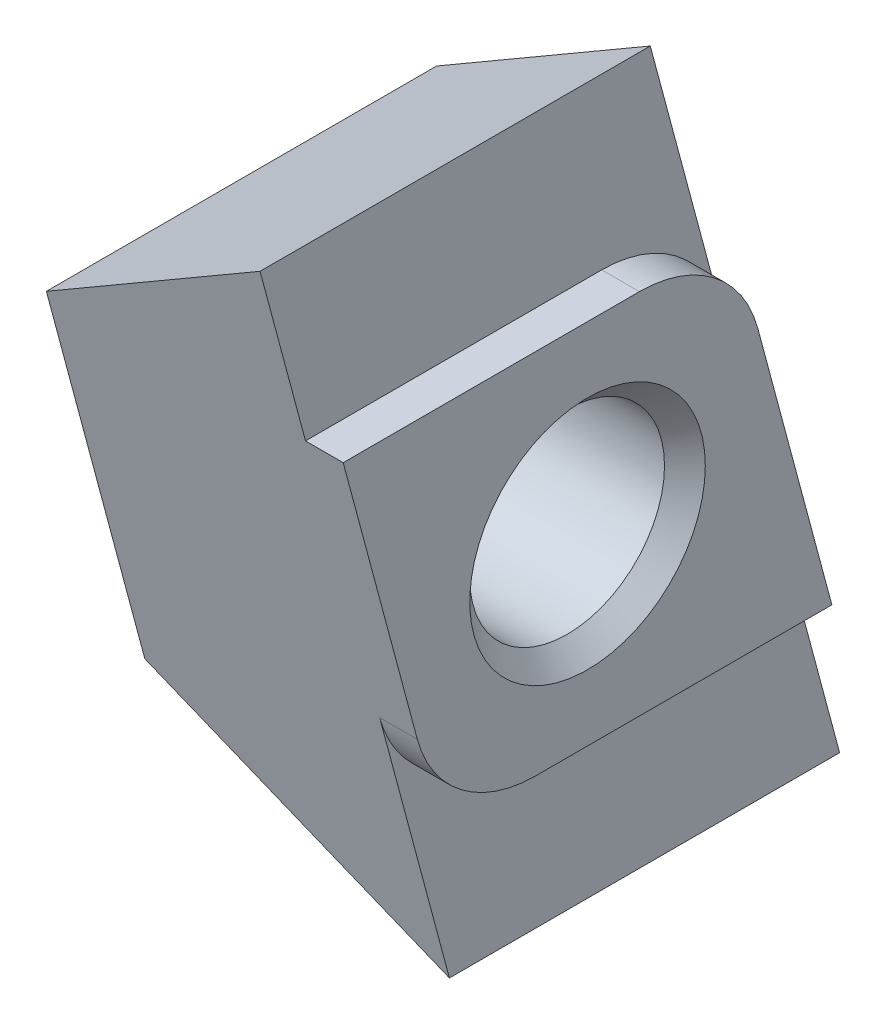
SolidWorks part; units mm, degrees
ref_plane "Piano frontale" through (0, 0, 0) normal (0, 0, 1) x (1, 0, 0)
ref_plane "Piano superiore" through (0, 0, 0) normal (0, 1, 0) x (1, 0, 0)
ref_plane "Piano destro" through (0, 0, 0) normal (1, 0, 0) x (0, 0, -1)
sketch "Sketch1" plane through (0, 0, 0) normal (1, 0, 0) x (0, 0, -1)
  line L0 (1.1011, 3.9) -> (-5.1861, 3.9)
  line L1 (-5.1861, 3.9) -> (-3.6125, -1.9729)
  line L2 (-1.1011, -3.9) -> (5.1861, -3.9)
  line L3 (5.1861, -3.9) -> (3.6125, 1.9729)
  arc A0 (-3.6125, -1.9729) -> (-1.1011, -3.9) centre (-1.1011, -1.3) ccw
  arc A1 (3.6125, 1.9729) -> (1.1011, 3.9) centre (1.1011, 1.3) ccw
extrude "Extrude1" add sketch "Sketch1" against normal blind 0.8
sketch "Sketch2" plane through (-0.8, 0, 0) normal (-1, 0, 0) x (0, 0, 1)
  line L0 (2.1315, -7.5) -> (-6.1507, -7.5)
  line L1 (-2.1315, 7.5) -> (6.1507, 7.5)
  spline S0 degree 3 poles (-2.1315, 7.5) (-3.4712, 2.5) (-4.811, -2.5) (-6.1507, -7.5) knots 0 0 0 0 1 1 1 1
  spline S1 degree 3 poles (2.1315, -7.5) (3.4712, -2.5) (4.811, 2.5) (6.1507, 7.5) knots 0 0 0 0 1 1 1 1
extrude "Extrude2" add sketch "Sketch2" along normal blind 5.5
draft "Draft1" type of draft neutral plane draft angle 33.207 faces to draft 1 face at (-3.55, 7.5, 2.0096) neutral plane through (-0.8, 0, 4.1411) neutral plane normal (1, 0, 0) reverse direction yes parameters "D1"=33.207
draft "Draft2" type of draft neutral plane draft angle 33.207 faces to draft 1 face at (-3.55, -7.5, -2.0096) neutral plane through (-0.8, 0, 4.1411) neutral plane normal (1, 0, 0) reverse direction yes parameters "D1"=33.207
hole_wizard "HoleWzd1" positions "Sketch4" profile "Sketch3" hole size "M3.5" standard "Ansi Metric" end condition through all
sketch "Sketch4" plane through (-6.3, 0, 0) normal (-1, 0, 0) x (0, 0, 1)
  point P0 (0, 0)
sketch "Sketch3" plane through (-6.3, 0, 0) normal (0, 1, 0) x (0, 0, 1)
  line L0 (0, 0) -> (0, 6.3)
  line L1 (0, 6.3) -> (2.067, 6.3)
  line L2 (2.067, 6.3) -> (2.067, 0)
  line L5 (2.067, 0) -> (0, 0)
  line L11 (0, -6.35) -> (0, 107.95) construction
  dimension "Thru Hole Dia." = 4.134
  dimension "Thru Hole Depth" = 6.3
chamfer "Chamfer1" distance 0.433 angle 45 2 edges at (0, 0, -2.067) (-6.3, 0, 2.067)
